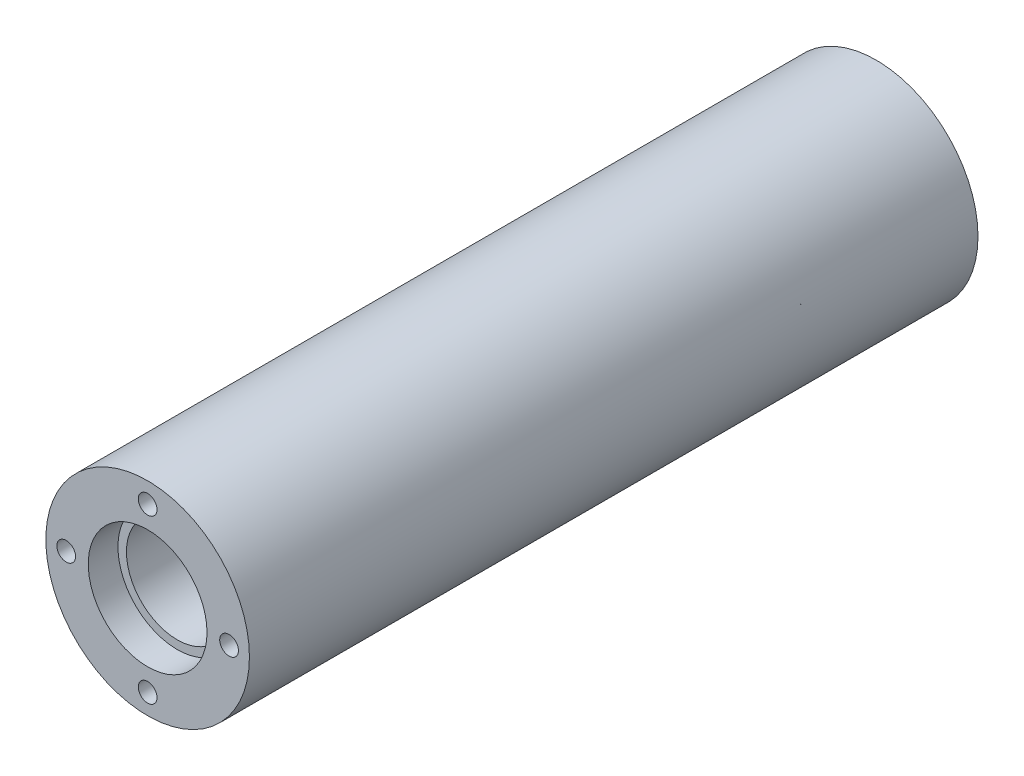
SolidWorks part; units mm, degrees
other "Markup1"
sketch "Sketch4" plane through (19.05, 19.05, 152.4) normal (0.8805, 0.4318, 0.1958) x (0.1841, 0.0692, -0.9805)
ref_plane "Front Plane" through (0, 0, 0) normal (0, 0, 1) x (1, 0, 0)
ref_plane "Top Plane" through (0, 0, 0) normal (0, 1, 0) x (1, 0, 0)
ref_plane "Right Plane" through (0, 0, 0) normal (1, 0, 0) x (0, 0, -1)
sketch "Sketch1" plane through (0, 0, 0) normal (0, 0, 1) x (1, 0, 0)
  circle A0 centre (0, 0) radius 19.05
  circle A1 centre (0, 0) radius 9.525
  dimension "D1" = 38.1
  dimension "D2" = 19.05
extrude "Boss-Extrude1" add sketch "Sketch1" along normal blind 136.3472
sketch "Sketch2" plane through (0, 0, 0) normal (0, 0, -1) x (-1, 0, 0)
  circle A0 centre (0, 15.24) radius 1.7526
  circle A1 centre (15.24, 0) radius 1.7526
  circle A2 centre (0, -15.24) radius 1.7526
  circle A3 centre (-15.24, 0) radius 1.7526
  point P12 (0, 0)
  dimension "D1" = 3.5052
  dimension "D2" = 15.24
  dimension "D3" = 4
extrude "Cut-Extrude1" cut sketch "Sketch2" against normal blind 9.525
sketch "Sketch3" plane through (0, 0, 136.3472) normal (0, 0, 1) x (1, 0, 0)
  circle A0 centre (0, 15.24) radius 1.7526
  circle A1 centre (15.24, 0) radius 1.7526
  circle A2 centre (0, -15.24) radius 1.7526
  circle A3 centre (-15.24, 0) radius 1.7526
  point P2 (0, 0)
  point P9 (0, 0)
  point P12 (0, 0)
  point P15 (0, 0)
  point P16 (0, 0)
  dimension "D2" = 3.5052
  dimension "D1" = 15.24
  dimension "D3" = 4
extrude "Cut-Extrude2" cut sketch "Sketch3" against normal blind 9.525
sketch "Sketch6" plane through (0, 0, 136.3472) normal (0, 0, 1) x (1, 0, 0)
  circle A0 centre (0, 0) radius 11.1125
  dimension "D1" = 22.225
extrude "Cut-Extrude3" cut sketch "Sketch6" against normal blind 5.5562
sketch "Sketch7" plane through (0, 0, 0) normal (0, 0, -1) x (-1, 0, 0)
  circle A0 centre (0, 0) radius 11.1125
  dimension "D1" = 22.225
extrude "Cut-Extrude4" cut sketch "Sketch7" against normal blind 5.5562
